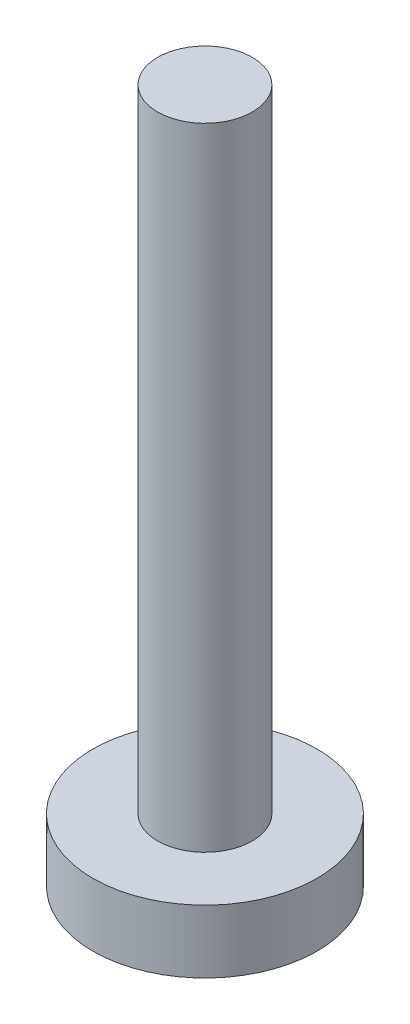
SolidWorks part; units mm, degrees
ref_plane "前视基准面" through (0, 0, 0) normal (0, 0, 1) x (1, 0, 0)
ref_plane "上视基准面" through (0, 0, 0) normal (0, 1, 0) x (1, 0, 0)
ref_plane "右视基准面" through (0, 0, 0) normal (1, 0, 0) x (0, 0, -1)
sketch "草图1" plane through (0, 0, 0) normal (0, 1, 0) x (1, 0, 0)
  circle A0 centre (0, 0) radius 3.55
  dimension "D1" = 7.1
extrude "凸台-拉伸1" add sketch "草图1" along normal blind 2
sketch "草图2" plane through (0, 2, 0) normal (0, 1, 0) x (1, 0, 0)
  circle A0 centre (0, 0) radius 1.5
  dimension "D1" = 3
extrude "凸台-拉伸2" add sketch "草图2" along normal blind 20
